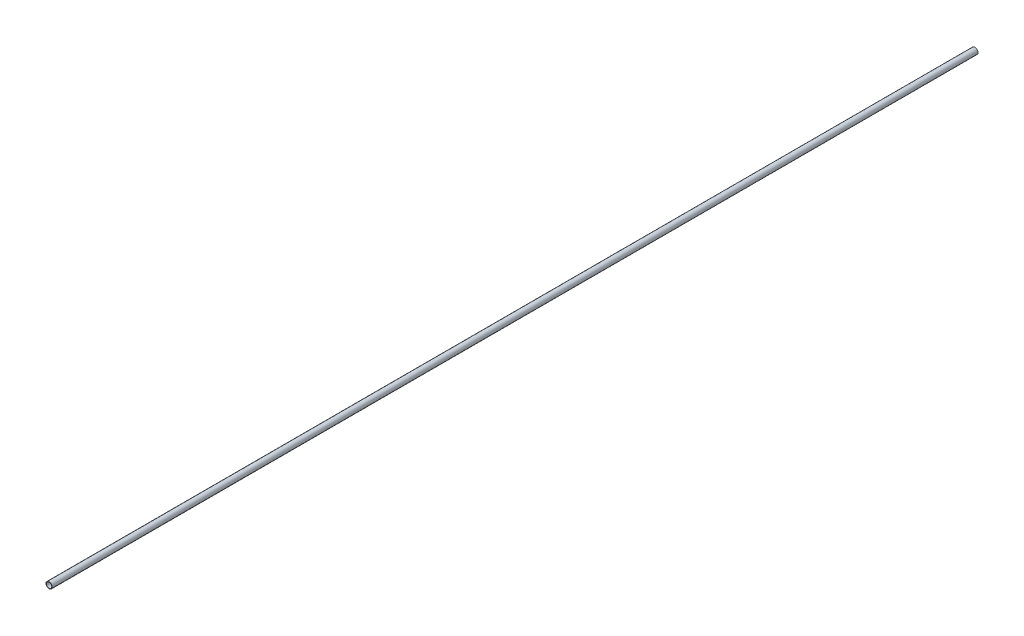
SolidWorks part; units mm, degrees
material "Alumina"
ref_plane "Front Plane" through (0, 0, 0) normal (0, 0, 1) x (1, 0, 0)
ref_plane "Top Plane" through (0, 0, 0) normal (0, 1, 0) x (1, 0, 0)
ref_plane "Right Plane" through (0, 0, 0) normal (1, 0, 0) x (0, 0, -1)
sketch "Sketch1" plane through (0, 0, 0) normal (0, 0, 1) x (1, 0, 0)
  circle A0 centre (0, 0) radius 3.5
  circle A1 centre (0, 0) radius 4
  dimension "D1" = 8
  dimension "D2" = 7
extrude "Boss-Extrude1" add sketch "Sketch1" along normal blind 1200
